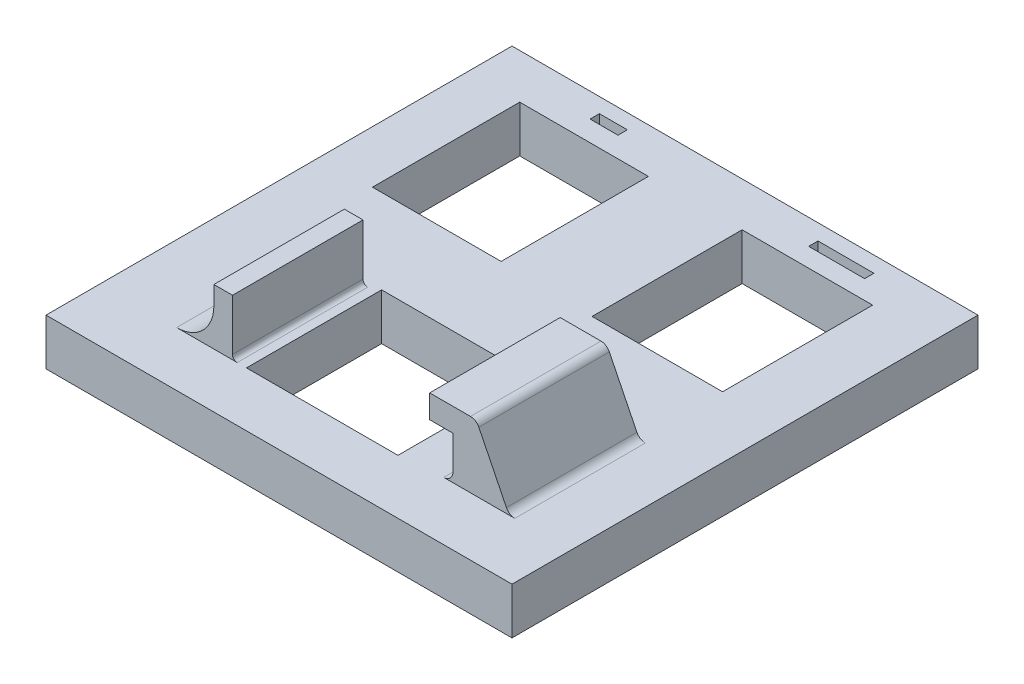
SolidWorks part; units mm, degrees
ref_plane "Front Plane" through (0, 0, 0) normal (0, 0, 1) x (1, 0, 0)
ref_plane "Top Plane" through (0, 0, 0) normal (0, 1, 0) x (1, 0, 0)
ref_plane "Right Plane" through (0, 0, 0) normal (1, 0, 0) x (0, 0, -1)
sketch "Sketch1" plane through (0, 0, 0) normal (0, 1, 0) x (1, 0, 0)
  line L1 (-25, 12.5) -> (25, 12.5)
  line L2 (-25, 12.5) -> (-25, -12.5)
  line L3 (-25, -12.5) -> (25, -12.5)
  line L4 (25, 12.5) -> (25, -12.5)
  line L5 (-25, 12.5) -> (25, -12.5) construction
  line L6 (-25, -12.5) -> (25, 12.5) construction
  point P0 (0, 0)
  dimension "D1" = 25
  dimension "D2" = 50
extrude "Boss-Extrude1" add sketch "Sketch1" along normal blind 5
sketch "Sketch2" plane through (0, 5, 0) normal (0, 1, 0) x (1, 0, 0)
  line L1 (-19.3716, 7.7037) -> (-5.5716, 7.7037)
  line L2 (-19.3716, 7.7037) -> (-19.3716, -8.0963)
  line L3 (-19.3716, -8.0963) -> (-5.5716, -8.0963)
  line L4 (-5.5716, 7.7037) -> (-5.5716, -8.0963)
  line L5 (-19.3716, 7.7037) -> (-5.5716, -8.0963) construction
  line L6 (-19.3716, -8.0963) -> (-5.5716, 7.7037) construction
  point P0 (-12.4716, -0.1963)
  dimension "D1" = 13.8
  dimension "D2" = 15.8
extrude "Cut-Extrude1" cut sketch "Sketch2" against normal blind 5 contours L2 L1 L4 L3
sketch "Sketch3" plane through (0, 5, 0) normal (0, 1, 0) x (1, 0, 0)
  line L1 (4.4189, 7.7737) -> (18.4189, 7.7737)
  line L2 (4.4189, 7.7737) -> (4.4189, -8.3263)
  line L3 (4.4189, -8.3263) -> (18.4189, -8.3263)
  line L4 (18.4189, 7.7737) -> (18.4189, -8.3263)
  line L5 (4.4189, 7.7737) -> (18.4189, -8.3263) construction
  line L6 (4.4189, -8.3263) -> (18.4189, 7.7737) construction
  point P0 (11.4189, -0.2763)
  dimension "D1" = 14
  dimension "D2" = 16.1
extrude "Cut-Extrude2" cut sketch "Sketch3" against normal blind 5
sketch "Sketch5" plane through (0, 5, 0) normal (0, 1, 0) x (1, 0, 0)
  line L1 (-14.0298, 10.9039) -> (-11.0298, 10.9039)
  line L2 (-14.0298, 10.9039) -> (-14.0298, 9.9039)
  line L3 (-14.0298, 9.9039) -> (-11.0298, 9.9039)
  line L4 (-11.0298, 10.9039) -> (-11.0298, 9.9039)
  line L5 (9.5287, 10.8029) -> (15.5287, 10.8029)
  line L6 (9.5287, 10.8029) -> (9.5287, 9.8029)
  line L7 (9.5287, 9.8029) -> (15.5287, 9.8029)
  line L8 (15.5287, 10.8029) -> (15.5287, 9.8029)
  dimension "D1" = 1
  dimension "D2" = 3
  dimension "D3" = 6
  dimension "D4" = 1
extrude "Cut-Extrude3" cut sketch "Sketch5" against normal blind 1
sketch "Sketch6" plane through (0, 0, 0) normal (0, 1, 0) x (1, 0, 0)
  line L1 (-25, -12.5) -> (25, -12.5)
  line L2 (-25, -12.5) -> (-25, -37.5)
  line L3 (-25, -37.5) -> (25, -37.5)
  line L4 (25, -12.5) -> (25, -37.5)
  dimension "D1" = 25
  dimension "D2" = 50
extrude "Boss-Extrude2" add sketch "Sketch6" along normal blind 5
sketch "Sketch7" plane through (0, 5, 0) normal (0, 1, 0) x (1, 0, 0)
  line L1 (6.9104, -17.149) -> (6.9104, -31.649)
  line L2 (6.9104, -17.149) -> (-9.3396, -17.149)
  line L3 (-9.3396, -17.149) -> (-9.3396, -31.649)
  line L4 (6.9104, -31.649) -> (-9.3396, -31.649)
  dimension "D1" = 14.5
  dimension "D2" = 16.25
extrude "Cut-Extrude4" cut sketch "Sketch7" against normal blind 4 contours L2 L1 L4 L3
sketch "Sketch8" plane through (0, 1, 0) normal (0, 1, 0) x (1, 0, 0)
  line L5 (6.9104, -17.149) -> (-9.3396, -17.149) construction
  line L6 (-9.3396, -31.649) -> (5.4104, -31.649)
  line L7 (-9.3396, -31.649) -> (-9.3396, -17.149)
  line L8 (-9.3396, -17.149) -> (5.4104, -17.149)
  line L9 (5.4104, -31.649) -> (5.4104, -17.149)
  dimension "D1" = 14.75
extrude "Cut-Extrude5" cut sketch "Sketch8" against normal blind 1
sketch "Sketch9" plane through (0, 5, 0) normal (0, 1, 0) x (1, 0, 0)
  line L5 (6.9104, -17.149) -> (6.9104, -31.649) construction
  line L6 (12.4104, -17.2424) -> (14.9104, -17.2424)
  line L7 (12.4104, -17.2424) -> (12.4104, -31.2424)
  line L8 (12.4104, -31.2424) -> (14.9104, -31.2424)
  line L9 (14.9104, -17.2424) -> (14.9104, -31.2424)
  dimension "D1" = 14
  dimension "D2" = 2.5
  dimension "D3" = 5.5
extrude "Boss-Extrude3" add sketch "Sketch9" along normal blind 4.6
sketch "Sketch10" plane through (0, 9.6, 0) normal (0, 1, 0) x (1, 0, 0)
  line L1 (14.9104, -17.2424) -> (9.9104, -17.2424)
  line L2 (14.9104, -17.2424) -> (14.9104, -31.2424)
  line L3 (14.9104, -31.2424) -> (9.9104, -31.2424)
  line L4 (9.9104, -17.2424) -> (9.9104, -31.2424)
  dimension "D1" = 14
  dimension "D2" = 5
extrude "Boss-Extrude4" add sketch "Sketch10" along normal blind 2.5
sketch "Sketch11" plane through (0, 0, 31.2424) normal (0, 0, 1) x (1, 0, 0)
  line L0 (14.9104, 5) -> (18.4189, 5)
  line L1 (18.4189, 5) -> (14.9104, 12.1)
  line L2 (14.9104, 12.1) -> (14.9104, 5)
extrude "Boss-Extrude5" add sketch "Sketch11" against normal blind 14
fillet "Fillet1" radius 1 2 edges at (18.4189, 5, 24.2424) (14.9104, 12.1, 24.2424)
sketch "Sketch12" plane through (0, 5, 0) normal (0, 1, 0) x (1, 0, 0)
  line L0 (-9.3396, -17.149) -> (-9.3396, -31.649) construction
  line L1 (-10.8396, -17.649) -> (-12.8396, -17.649)
  line L2 (-10.8396, -17.649) -> (-10.8396, -31.649)
  line L3 (-10.8396, -31.649) -> (-12.8396, -31.649)
  line L4 (-12.8396, -17.649) -> (-12.8396, -31.649)
  line L5 (6.9104, -31.649) -> (-9.3396, -31.649) construction
  dimension "D1" = 14
  dimension "D2" = 2
  dimension "D3" = 1.5
extrude "Boss-Extrude6" add sketch "Sketch12" along normal blind 6
fillet "Fillet2" radius 4 1 edges at (-12.8396, 5, 24.649)
fillet "Fillet3" radius 1 1 edges at (12.4104, 5, 24.2424)
fillet "Fillet4" radius 0.5 1 edges at (-10.8396, 5, 24.649)
